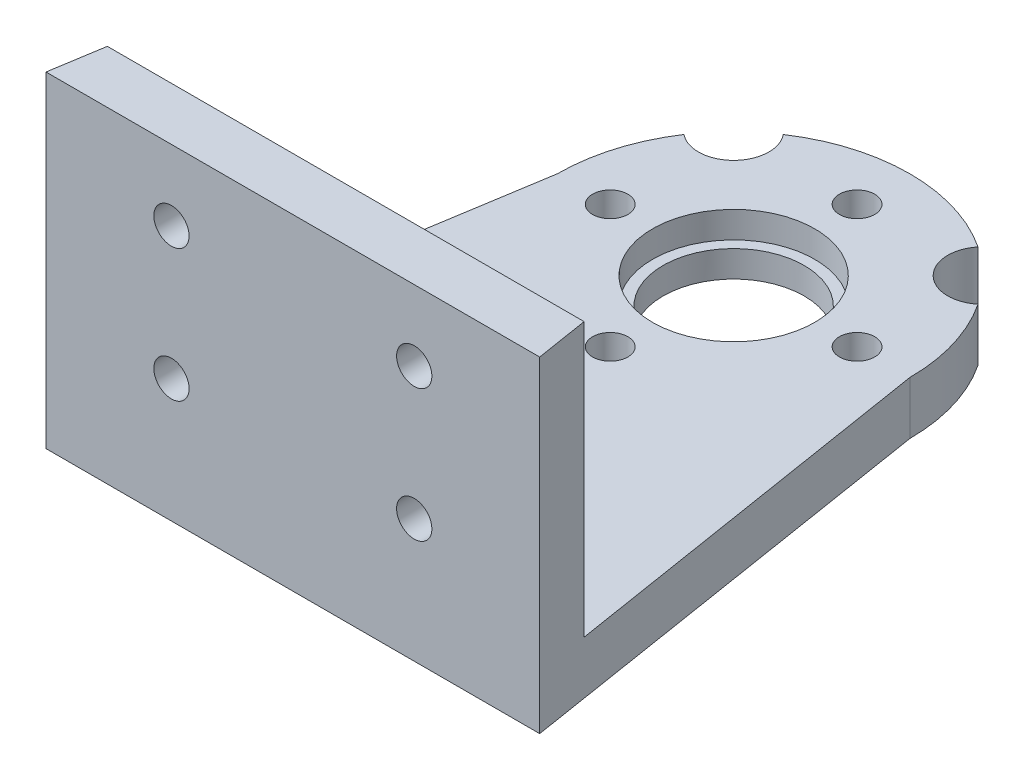
SolidWorks part; units mm, degrees
material "Custom Plastic"
ref_plane "Front Plane" through (0, 0, 0) normal (0, 0, 1) x (1, 0, 0)
ref_plane "Top Plane" through (0, 0, 0) normal (0, 1, 0) x (1, 0, 0)
ref_plane "Right Plane" through (0, 0, 0) normal (1, 0, 0) x (0, 0, -1)
sketch "Sketch1" plane through (0, 0, 0) normal (0, 1, 0) x (1, 0, 0)
  line L0 (-10, 0) -> (-14, -25)
  line L1 (10, 0) -> (14, -25)
  line L2 (0, 17.2103) -> (0, -39.4896) construction
  line L3 (-14, -25) -> (14, -25)
  arc A0 (-10, 0) -> (10, 0) centre (0, 0) cw
  dimension "D1" = 10
  dimension "D2" = 25
  dimension "D3" = 14
extrude "Boss-Extrude1" add sketch "Sketch1" along normal blind 3
sketch "Sketch2" plane through (0, 3, 0) normal (0, 1, 0) x (1, 0, 0)
  line L0 (-21.4034, 0) -> (30.5216, 0) construction
  circle A0 centre (0, 0) radius 4
  dimension "D1" = 8
extrude "Cut-Extrude1" cut sketch "Sketch2" against normal blind 13
sketch "Sketch3" plane through (0, 3, 0) normal (0, 1, 0) x (1, 0, 0)
  line L0 (0, 14.8087) -> (0, -39.0944) construction
  line L1 (-14, -25) -> (14, -25) construction
  line L2 (-10, 0) -> (0, 0) construction
  line L3 (-13.04, -19) -> (0, -19) construction
  line L4 (-10, 0) -> (-14, -25) construction
  line L5 (14, -25) -> (10, 0) construction
  circle A0 centre (-6.52, -19) radius 1
  circle A1 centre (6.52, -19) radius 1
  circle A2 centre (0, -19) radius 1
  point P3 (-6.52, -19)
  point P11 (-13.04, -19)
  point P12 (13.0353, -18.9708)
  point P18 (0, -19)
  dimension "D3" = 2
  dimension "D2" = 2
  dimension "D1" = 6
extrude "Cut-Extrude2" cut sketch "Sketch3" against normal blind 13
sketch "Sketch4" plane through (0, 3, 0) normal (0, 1, 0) x (1, 0, 0)
  line L0 (0, 11.5358) -> (0, -14.2328) construction
  circle A0 centre (0, -7) radius 1
  circle A1 centre (-7, 0) radius 1
  circle A2 centre (0, 7) radius 1
  circle A3 centre (7, 0) radius 1
  point P0 (0, -7)
  point P15 (0, 0)
  dimension "D2" = 2
  dimension "D1" = 7
  dimension "D3" = 4
extrude "Cut-Extrude3" cut sketch "Sketch4" against normal up to vertex (3 mm away) up to point (0, 0, 0)
sketch "Sketch5" plane through (0, 3, 0) normal (0, 1, 0) x (1, 0, 0)
  line L0 (-13.52, -22) -> (13.52, -22)
  line L1 (-10, 0) -> (-14, -25) construction
  line L2 (14, -25) -> (10, 0) construction
  line L3 (-13.52, -22) -> (-14, -25)
  line L4 (-14, -25) -> (14, -25)
  line L5 (14, -25) -> (13.52, -22)
  dimension "D1" = 3
extrude "Boss-Extrude2" add sketch "Sketch5" along normal blind 15.5
sketch "Sketch6" plane through (0, 3, 0) normal (0, 1, 0) x (1, 0, 0)
  circle A0 centre (0, 0) radius 4.6
  dimension "D1" = 9.2
extrude "Cut-Extrude4" cut sketch "Sketch6" against normal blind 1.5
sketch "Sketch7" plane through (0, 3, 0) normal (0, 1, 0) x (1, 0, 0)
  line L0 (0, 12.0905) -> (0, -12.7025) construction
  line L1 (-13.0501, 13.0501) -> (0, 0) construction
  circle A0 centre (-7.0711, 7.0711) radius 2
  arc A1 (10, 0) -> (-10, 0) centre (0, 0) ccw construction
  circle A2 centre (7.0711, 7.0711) radius 2
  dimension "D1" = 4
extrude "Cut-Extrude5" cut sketch "Sketch7" against normal blind 10
sketch "Sketch8" plane through (0, 0, 22) normal (0, 0, -1) x (-1, 0, 0)
  line L0 (13.52, 14.5) -> (-13.52, 14.5) construction
  line L1 (13.52, 18.5) -> (13.52, 3) construction
  line L2 (-13.52, 18.5) -> (-13.52, 3) construction
  line L3 (-13.52, 18.5) -> (13.52, 18.5) construction
  circle A0 centre (6.885, 14.5) radius 1
  circle A1 centre (-6.885, 14.5) radius 1
  circle A2 centre (6.885, 7) radius 1
  circle A3 centre (-6.885, 7) radius 1
  dimension "D2" = 2
  dimension "D3" = 2
  dimension "D1" = 13.77
  dimension "D4" = 6.635
  dimension "D6" = 4
  dimension "D5" = 2
extrude "Cut-Extrude6" cut sketch "Sketch8" against normal blind 10
